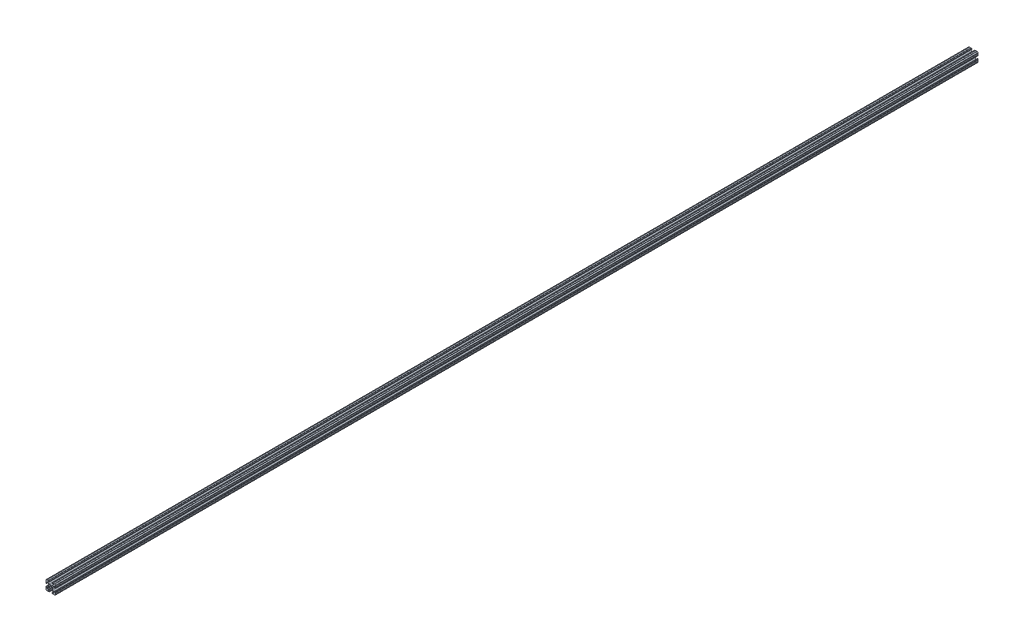
SolidWorks part; units mm, degrees
ref_plane "Front Plane" through (0, 0, 0) normal (0, 0, 1) x (1, 0, 0)
ref_plane "Top Plane" through (0, 0, 0) normal (0, 1, 0) x (1, 0, 0)
ref_plane "Right Plane" through (0, 0, 0) normal (1, 0, 0) x (0, 0, -1)
sketch "Sketch1" plane through (0, 0, 0) normal (0, 0, 1) x (1, 0, 0)
  line L0 (-1.7093, -4.4958) -> (1.7093, -4.4958)
  line L1 (3.9523, -5.4237) -> (7.1797, -8.6452)
  line L2 (6.4164, -10.4902) -> (4.2875, -10.4902)
  line L3 (3.2385, -11.5392) -> (3.2385, -11.651)
  line L4 (4.2875, -12.7) -> (5.3171, -12.7)
  line L5 (6.3331, -12.7) -> (9.5504, -12.7)
  line L6 (12.7, -9.5504) -> (12.7, -6.3331)
  line L7 (12.7, -5.3171) -> (12.7, -4.2875)
  line L8 (11.651, -3.2385) -> (11.5392, -3.2385)
  line L9 (10.4902, -4.2875) -> (10.4902, -6.4021)
  line L10 (8.7371, -7.1294) -> (5.441, -3.8408)
  line L11 (4.5085, -1.5932) -> (4.5085, 1.5932)
  line L12 (5.441, 3.8408) -> (8.7371, 7.1294)
  line L13 (10.4902, 6.4021) -> (10.4902, 4.2875)
  line L14 (11.5392, 3.2385) -> (11.651, 3.2385)
  line L15 (12.7, 4.2875) -> (12.7, 5.3171)
  line L16 (12.7, 6.3331) -> (12.7, 9.5504)
  line L17 (9.5504, 12.7) -> (6.3331, 12.7)
  line L18 (5.3171, 12.7) -> (4.2875, 12.7)
  line L19 (3.2385, 11.651) -> (3.2385, 11.5392)
  line L20 (4.2875, 10.4902) -> (6.4768, 10.4902)
  line L21 (7.207, 8.7244) -> (3.8983, 5.4232)
  line L22 (1.6558, 4.4958) -> (-1.6558, 4.4958)
  line L23 (-3.8983, 5.4232) -> (-7.207, 8.7244)
  line L24 (-6.4768, 10.4902) -> (-4.2875, 10.4902)
  line L25 (-3.2385, 11.5392) -> (-3.2385, 11.651)
  line L26 (-4.2875, 12.7) -> (-5.3171, 12.7)
  line L27 (-6.3331, 12.7) -> (-9.5504, 12.7)
  line L28 (-12.7, 9.5504) -> (-12.7, 6.3331)
  line L29 (-12.7, 5.3171) -> (-12.7, 4.2875)
  line L30 (-11.651, 3.2385) -> (-11.5392, 3.2385)
  line L31 (-10.4902, 4.2875) -> (-10.4902, 6.4021)
  line L32 (-8.7371, 7.1294) -> (-5.441, 3.8408)
  line L33 (-4.5085, 1.5932) -> (-4.5085, -1.5932)
  line L34 (-5.441, -3.8408) -> (-8.7371, -7.1294)
  line L35 (-10.4902, -6.4021) -> (-10.4902, -4.2875)
  line L36 (-11.5392, -3.2385) -> (-11.651, -3.2385)
  line L37 (-12.7, -4.2875) -> (-12.7, -5.3171)
  line L38 (-12.7, -6.3331) -> (-12.7, -9.5504)
  line L39 (-9.5504, -12.7) -> (-6.3331, -12.7)
  line L40 (-5.3171, -12.7) -> (-4.2875, -12.7)
  line L41 (-3.2385, -11.651) -> (-3.2385, -11.5392)
  line L42 (-4.2875, -10.4902) -> (-6.4164, -10.4902)
  line L43 (-7.1797, -8.6452) -> (-3.9523, -5.4237)
  line L44 (0, 0) -> (0, 2.5)
  line L45 (0, 0) -> (-2.5, 0)
  line L46 (0, 0) -> (0, -2.5)
  line L47 (0, 0) -> (2.5, 0)
  line L48 (0, 5) -> (0, 5.1035)
  line L49 (-5, 0) -> (-5.1035, 0)
  line L50 (0, -5) -> (0, -5.1035)
  line L51 (5, 0) -> (5.1035, 0)
  line L101 (-115.9492, 3668.6391) -> (-116.9788, 3668.6391)
  line L103 (-114.9001, 3668.6391) -> (-115.9492, 3668.6391)
  line L107 (-122.2281, 3668.6391) -> (-124.3615, 3668.6391)
  line L111 (-98.9618, 3668.6391) -> (-101.0952, 3668.6391)
  line L116 (-121.2121, 3668.6391) -> (-122.2281, 3668.6391)
  line L119 (-106.3445, 3668.6391) -> (-107.3741, 3668.6391)
  line L122 (-117.9948, 3668.6391) -> (-121.2121, 3668.6391)
  line L124 (-116.9788, 3668.6391) -> (-117.9948, 3668.6391)
  line L127 (-101.0952, 3668.6391) -> (-102.1112, 3668.6391)
  line L130 (-105.3285, 3668.6391) -> (-106.3445, 3668.6391)
  line L132 (-102.1112, 3668.6391) -> (-105.3285, 3668.6391)
  line L135 (-107.3741, 3668.6391) -> (-108.4231, 3668.6391)
  line L139 (-108.4231, 3668.6391) -> (-110.0059, 3668.6391)
  line L141 (-113.3174, 3668.6391) -> (-114.9001, 3668.6391)
  line L143 (-110.0059, 3668.6391) -> (-113.3174, 3668.6391)
  circle A0 centre (0, 0) radius 2.6035
  arc A1 (3.9523, -5.4237) -> (1.7093, -4.4958) centre (1.7093, -7.6708) ccw
  arc A2 (6.4164, -10.4902) -> (7.1797, -8.6452) centre (6.4164, -9.4098) ccw
  arc A3 (4.2875, -10.4902) -> (3.2385, -11.5392) centre (4.2875, -11.5392) ccw
  arc A4 (3.2385, -11.651) -> (4.2875, -12.7) centre (4.2875, -11.651) ccw
  arc A5 (6.3331, -12.7) -> (5.3171, -12.7) centre (5.8251, -12.7) ccw
  arc A6 (10.5664, -12.6998) -> (9.5504, -12.7) centre (10.0584, -12.7) ccw
  arc A7 (10.5664, -12.6998) -> (12.6998, -10.5664) centre (10.5918, -10.5918) ccw
  arc A8 (12.7, -9.5504) -> (12.6998, -10.5664) centre (12.7, -10.0584) ccw
  arc A9 (12.7, -5.3171) -> (12.7, -6.3331) centre (12.7, -5.8251) ccw
  arc A10 (12.7, -4.2875) -> (11.651, -3.2385) centre (11.651, -4.2875) ccw
  arc A11 (11.5392, -3.2385) -> (10.4902, -4.2875) centre (11.5392, -4.2875) ccw
  arc A12 (8.7371, -7.1294) -> (10.4902, -6.4021) centre (9.4628, -6.4021) ccw
  arc A13 (4.5085, -1.5932) -> (5.441, -3.8408) centre (7.6835, -1.5932) ccw
  arc A14 (5.441, 3.8408) -> (4.5085, 1.5932) centre (7.6835, 1.5932) ccw
  arc A15 (10.4902, 6.4021) -> (8.7371, 7.1294) centre (9.4628, 6.4021) ccw
  arc A16 (10.4902, 4.2875) -> (11.5392, 3.2385) centre (11.5392, 4.2875) ccw
  arc A17 (11.651, 3.2385) -> (12.7, 4.2875) centre (11.651, 4.2875) ccw
  arc A18 (12.7, 6.3331) -> (12.7, 5.3171) centre (12.7, 5.8251) ccw
  arc A19 (12.6998, 10.5664) -> (12.7, 9.5504) centre (12.7, 10.0584) ccw
  arc A20 (12.6998, 10.5664) -> (10.5664, 12.6998) centre (10.5918, 10.5918) ccw
  arc A21 (9.5504, 12.7) -> (10.5664, 12.6998) centre (10.0584, 12.7) ccw
  arc A22 (5.3171, 12.7) -> (6.3331, 12.7) centre (5.8251, 12.7) ccw
  arc A23 (4.2875, 12.7) -> (3.2385, 11.651) centre (4.2875, 11.651) ccw
  arc A24 (3.2385, 11.5392) -> (4.2875, 10.4902) centre (4.2875, 11.5392) ccw
  arc A25 (7.207, 8.7244) -> (6.4768, 10.4902) centre (6.4768, 9.4563) ccw
  arc A26 (1.6558, 4.4958) -> (3.8983, 5.4232) centre (1.6558, 7.6708) ccw
  arc A27 (-3.8983, 5.4232) -> (-1.6558, 4.4958) centre (-1.6558, 7.6708) ccw
  arc A28 (-6.4768, 10.4902) -> (-7.207, 8.7244) centre (-6.4768, 9.4563) ccw
  arc A29 (-4.2875, 10.4902) -> (-3.2385, 11.5392) centre (-4.2875, 11.5392) ccw
  arc A30 (-3.2385, 11.651) -> (-4.2875, 12.7) centre (-4.2875, 11.651) ccw
  arc A31 (-6.3331, 12.7) -> (-5.3171, 12.7) centre (-5.8251, 12.7) ccw
  arc A32 (-10.5664, 12.6998) -> (-9.5504, 12.7) centre (-10.0584, 12.7) ccw
  arc A33 (-10.5664, 12.6998) -> (-12.6998, 10.5664) centre (-10.5918, 10.5918) ccw
  arc A34 (-12.7, 9.5504) -> (-12.6998, 10.5664) centre (-12.7, 10.0584) ccw
  arc A35 (-12.7, 5.3171) -> (-12.7, 6.3331) centre (-12.7, 5.8251) ccw
  arc A36 (-12.7, 4.2875) -> (-11.651, 3.2385) centre (-11.651, 4.2875) ccw
  arc A37 (-11.5392, 3.2385) -> (-10.4902, 4.2875) centre (-11.5392, 4.2875) ccw
  arc A38 (-8.7371, 7.1294) -> (-10.4902, 6.4021) centre (-9.4628, 6.4021) ccw
  arc A39 (-4.5085, 1.5932) -> (-5.441, 3.8408) centre (-7.6835, 1.5932) ccw
  arc A40 (-5.441, -3.8408) -> (-4.5085, -1.5932) centre (-7.6835, -1.5932) ccw
  arc A41 (-10.4902, -6.4021) -> (-8.7371, -7.1294) centre (-9.4628, -6.4021) ccw
  arc A42 (-10.4902, -4.2875) -> (-11.5392, -3.2385) centre (-11.5392, -4.2875) ccw
  arc A43 (-11.651, -3.2385) -> (-12.7, -4.2875) centre (-11.651, -4.2875) ccw
  arc A44 (-12.7, -6.3331) -> (-12.7, -5.3171) centre (-12.7, -5.8251) ccw
  arc A45 (-12.6998, -10.5664) -> (-12.7, -9.5504) centre (-12.7, -10.0584) ccw
  arc A46 (-12.6998, -10.5664) -> (-10.5664, -12.6998) centre (-10.5918, -10.5918) ccw
  arc A47 (-9.5504, -12.7) -> (-10.5664, -12.6998) centre (-10.0584, -12.7) ccw
  arc A48 (-5.3171, -12.7) -> (-6.3331, -12.7) centre (-5.8251, -12.7) ccw
  arc A49 (-4.2875, -12.7) -> (-3.2385, -11.651) centre (-4.2875, -11.651) ccw
  arc A50 (-3.2385, -11.5392) -> (-4.2875, -10.4902) centre (-4.2875, -11.5392) ccw
  arc A51 (-7.1797, -8.6452) -> (-6.4164, -10.4902) centre (-6.4164, -9.4098) ccw
  arc A52 (-1.7093, -4.4958) -> (-3.9523, -5.4237) centre (-1.7093, -7.6708) ccw
extrude "Boss-Extrude1" add sketch "Sketch1" along normal blind 2463.8 contours A52 L0 A1 L1 A2 L2 A3 L3 A4 L4 A5 L5 A6 A7 A8 L6 A9 L7 A10 L8 A11 L9 A12 L10 A13 L11 A14 L12 A15 L13 A16 L14 A17 L15 A18 L16 A19 A20 A21 L17 A22 L18 A23 L19 A24 L20 A25 L21 A26 L22 A27
